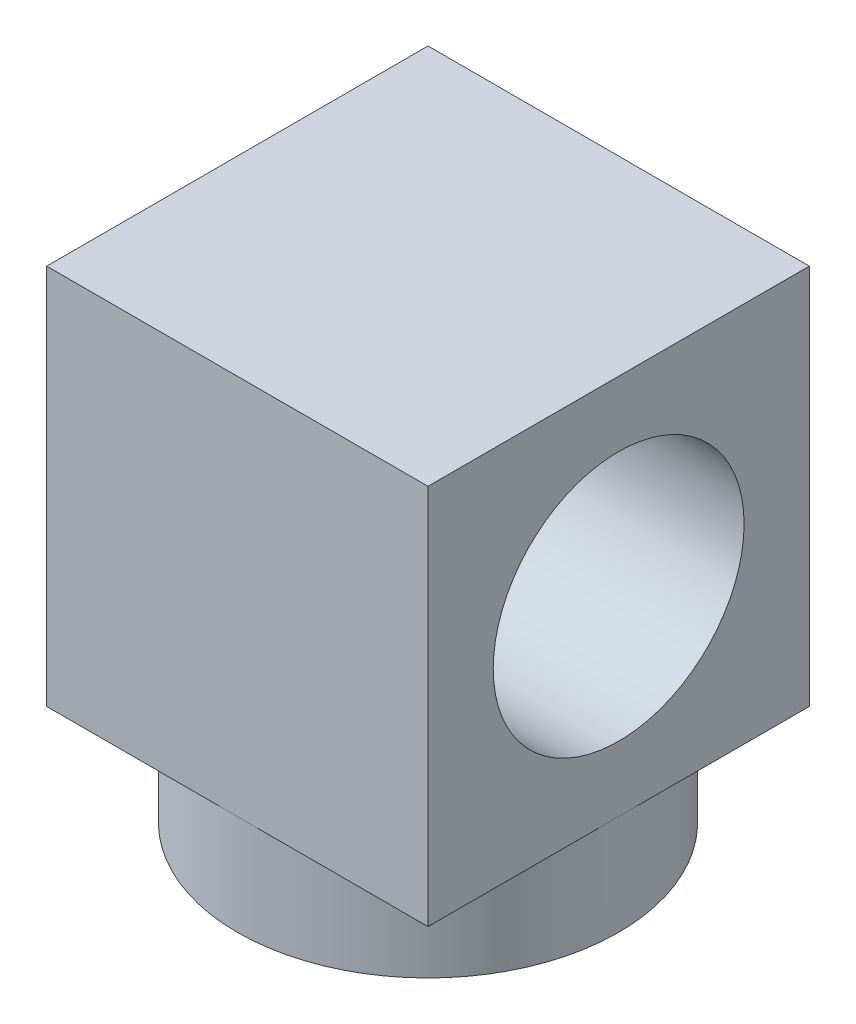
SolidWorks part; units mm, degrees
ref_plane "Front Plane" through (0, 0, 0) normal (0, 0, 1) x (1, 0, 0)
ref_plane "Top Plane" through (0, 0, 0) normal (0, 1, 0) x (1, 0, 0)
ref_plane "Right Plane" through (0, 0, 0) normal (1, 0, 0) x (0, 0, -1)
sketch "Sketch1" plane through (0, 0, 0) normal (0, 1, 0) x (1, 0, 0)
  circle A0 centre (0, 0) radius 4.826
extrude "Boss-Extrude1" add sketch "Sketch1" along normal blind 2.54
sketch "Sketch2" plane through (0, 2.54, 0) normal (0, 1, 0) x (1, 0, 0)
  line L1 (4.826, 4.826) -> (-4.826, 4.826)
  line L2 (4.826, 4.826) -> (4.826, -4.826)
  line L3 (4.826, -4.826) -> (-4.826, -4.826)
  line L4 (-4.826, 4.826) -> (-4.826, -4.826)
  line L5 (4.826, 4.826) -> (-4.826, -4.826) construction
  line L6 (4.826, -4.826) -> (-4.826, 4.826) construction
  point P0 (0, 0)
extrude "Boss-Extrude2" add sketch "Sketch2" along normal blind 9.652
sketch "Sketch3" plane through (4.826, 0, 0) normal (1, 0, 0) x (0, 0, -1)
  line L0 (-4.826, 7.366) -> (4.826, 7.366)
  line L1 (-4.826, 12.192) -> (-4.826, 2.54) construction
  line L2 (4.826, 12.192) -> (4.826, 2.54) construction
  circle A0 centre (0, 7.366) radius 3.175
extrude "Cut-Extrude1" cut sketch "Sketch3" against normal blind 9.652 contours A0
